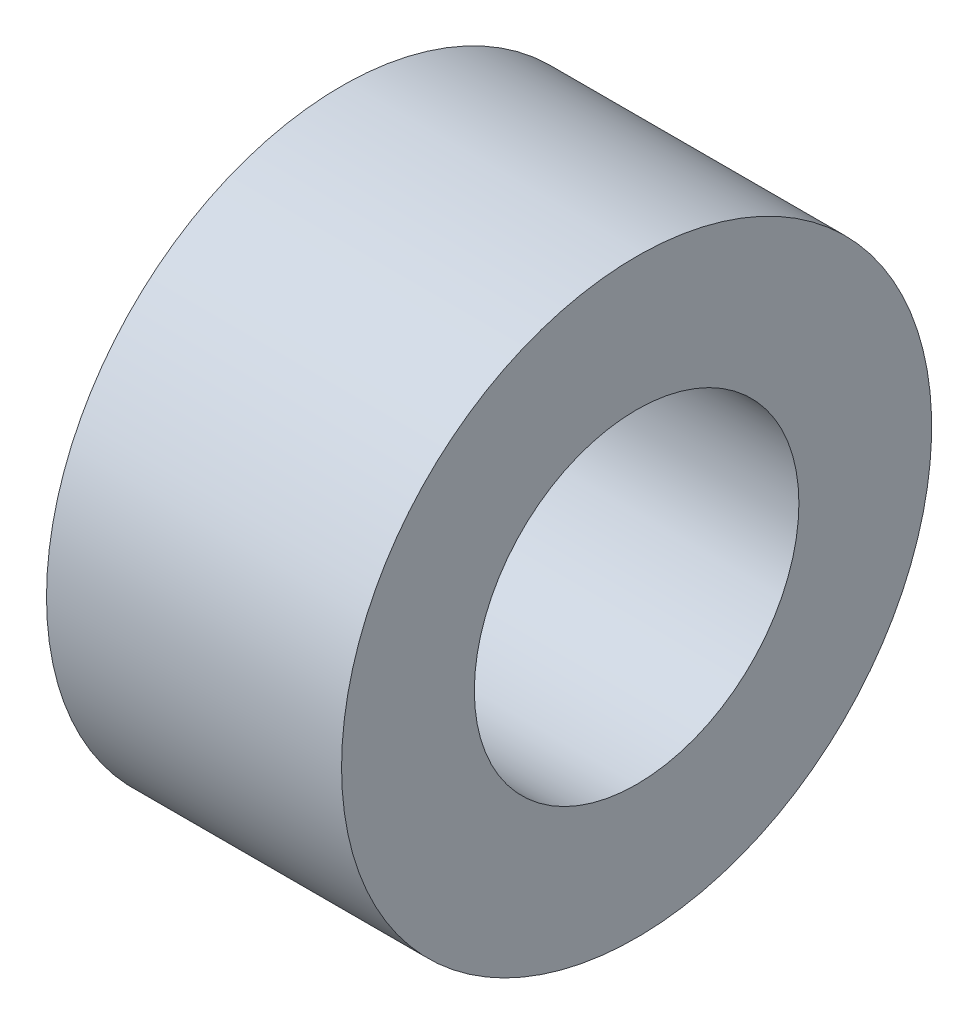
SolidWorks part; units mm, degrees
material "Contreplaqué pin"
ref_plane "Plan de face" through (0, 0, 0) normal (0, 0, 1) x (1, 0, 0)
ref_plane "Plan de dessus" through (0, 0, 0) normal (0, 1, 0) x (1, 0, 0)
ref_plane "Plan de droite" through (0, 0, 0) normal (1, 0, 0) x (0, 0, -1)
sketch "Esquisse1" plane through (0, 0, 0) normal (0, 0, 1) x (1, 0, 0)
  line L0 (0, 0) -> (5, 0) construction
  line L1 (0, 2.75) -> (5, 2.75)
  line L2 (0, 2.75) -> (0, 5)
  line L3 (0, 5) -> (5, 5)
  line L4 (5, 2.75) -> (5, 5)
  dimension "D1" = 2.75
  dimension "D2" = 5
  dimension "D3" = 5
revolve "Révolution1" add sketch "Esquisse1" angle 360 about L0
